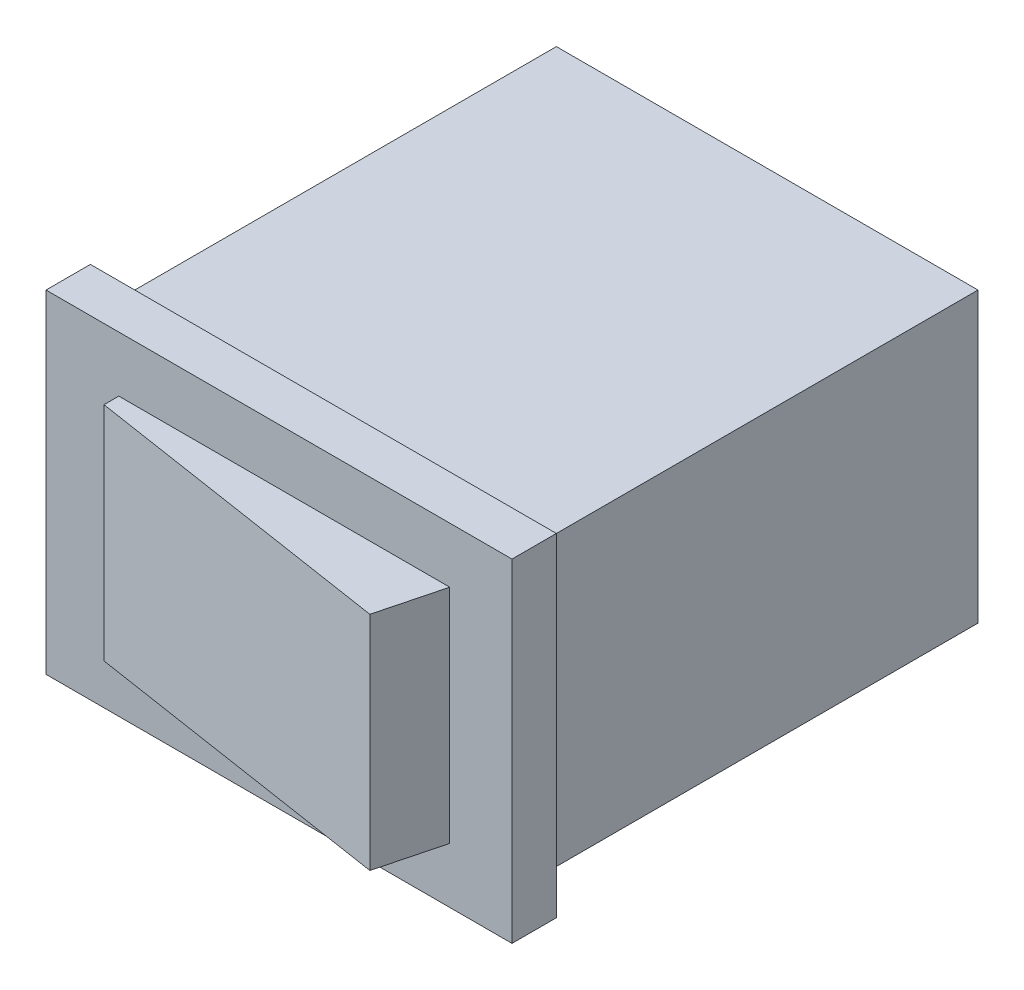
SolidWorks part; units mm, degrees
ref_plane "Front Plane" through (0, 0, 0) normal (0, 0, 1) x (1, 0, 0)
ref_plane "Top Plane" through (0, 0, 0) normal (0, 1, 0) x (1, 0, 0)
ref_plane "Right Plane" through (0, 0, 0) normal (1, 0, 0) x (0, 0, -1)
sketch "Sketch1" plane through (0, 0, 0) normal (0, 0, 1) x (1, 0, 0)
  line L1 (-9.5, 6.5) -> (9.5, 6.5)
  line L2 (-9.5, 6.5) -> (-9.5, -6.5)
  line L3 (-9.5, -6.5) -> (9.5, -6.5)
  line L4 (9.5, 6.5) -> (9.5, -6.5)
  line L5 (-9.5, 6.5) -> (9.5, -6.5) construction
  line L6 (-9.5, -6.5) -> (9.5, 6.5) construction
  point P0 (0, 0)
  dimension "D1" = 19
  dimension "D2" = 13
extrude "Boss-Extrude1" add sketch "Sketch1" along normal blind 20
sketch "Sketch2" plane through (0, 0, 20) normal (0, 0, 1) x (1, 0, 0)
  line L1 (-10.5, 7.5) -> (10.5, 7.5)
  line L2 (-10.5, 7.5) -> (-10.5, -7.5)
  line L3 (-10.5, -7.5) -> (10.5, -7.5)
  line L4 (10.5, 7.5) -> (10.5, -7.5)
  line L5 (-10.5, 7.5) -> (10.5, -7.5) construction
  line L6 (-10.5, -7.5) -> (10.5, 7.5) construction
  point P0 (0, 0)
  dimension "D1" = 15
  dimension "D2" = 21
extrude "Boss-Extrude2" add sketch "Sketch2" along normal blind 2
sketch "Sketch3" plane through (0, 0, 0) normal (0, 1, 0) x (1, 0, 0)
  line L0 (-7.2187, -22) -> (-7.2187, -22.6691)
  line L1 (10.5, -22) -> (-10.5, -22) construction
  line L2 (-7.2187, -22.6691) -> (6.9527, -24.8579)
  line L3 (6.9527, -24.8579) -> (7.6946, -22)
  line L4 (7.6946, -22) -> (-7.2187, -22)
extrude "Boss-Extrude3" add sketch "Sketch3" along normal blind 5 and the other way blind 5
